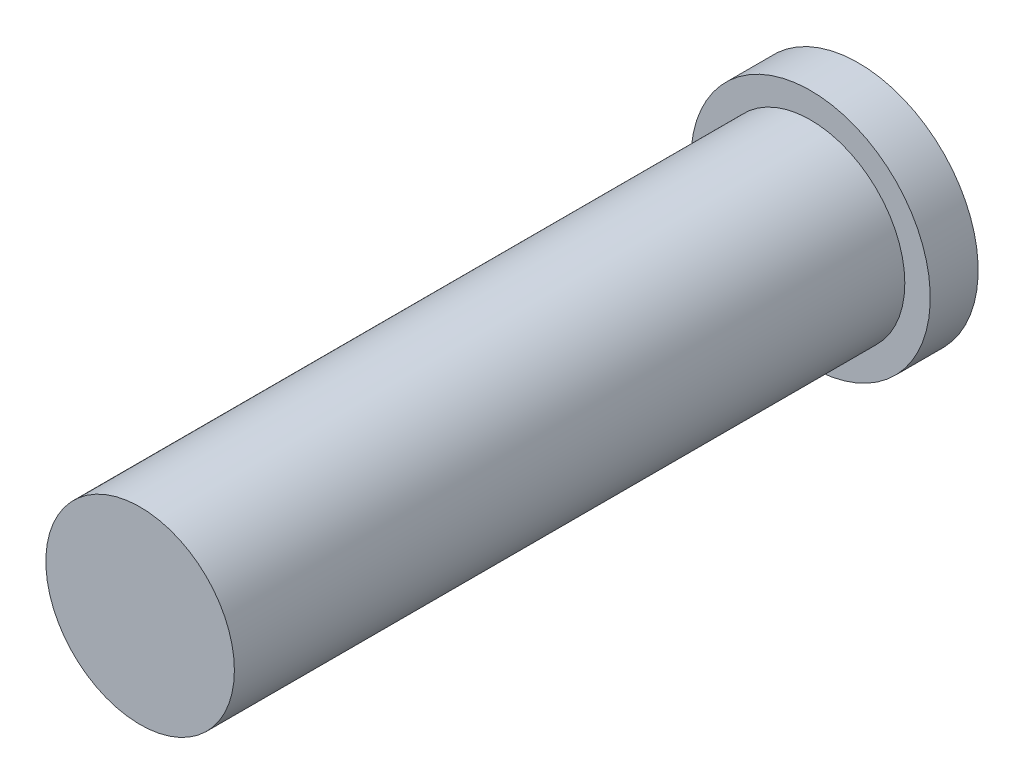
SolidWorks part; units mm, degrees
material "ABS"
ref_plane "Front Plane" through (0, 0, 0) normal (0, 0, 1) x (1, 0, 0)
ref_plane "Top Plane" through (0, 0, 0) normal (0, 1, 0) x (1, 0, 0)
ref_plane "Right Plane" through (0, 0, 0) normal (1, 0, 0) x (0, 0, -1)
sketch "Sketch1" plane through (0, 0, 0) normal (0, 0, 1) x (1, 0, 0)
  line L0 (11.0746, 1.623) -> (15.0746, 1.623) construction
  line L1 (15.5154, 2.1638) -> (14.2772, -0.5687)
  arc A1 (15.5154, 2.1638) -> (14.2772, -0.5687) centre (13.0746, 1.623) ccw
  point P10 (15.5154, 2.1638)
  point P13 (14.2772, -0.5687)
sketch "Sketch2" plane through (0, 0, 0) normal (0, 0, 1) x (1, 0, 0)
  circle A0 centre (13.0746, 1.623) radius 5
extrude "Boss-Extrude1" add sketch "Sketch2" along normal blind 35.56
extrude "Cut-Extrude1" cut sketch "Sketch1" along normal blind 25.4 and the other way through all contours A1 L1
sketch "Sketch3" plane through (0, 0, 0) normal (0, 0, -1) x (-1, 0, 0)
  circle A0 centre (-13.0746, 1.623) radius 6.35
extrude "Boss-Extrude2" add sketch "Sketch3" along normal blind 2.54
sketch "Sketch4" plane through (0, 0, -2.54) normal (0, 0, -1) x (-1, 0, 0)
  line L1 (-15.5154, 2.1638) -> (-14.2772, -0.5687)
  line L2 (-15.5154, 2.1638) -> (-14.2772, -0.5687)
  arc A1 (-14.2772, -0.5687) -> (-15.5154, 2.1638) centre (-13.0746, 1.623) ccw
  arc A2 (-14.2772, -0.5687) -> (-15.5154, 2.1638) centre (-13.0746, 1.623) ccw
  dimension "D1" = 0
extrude "Cut-Extrude2" cut sketch "Sketch4" against normal blind 2.54
sketch "Sketch5" plane through (0, 0, -2.54) normal (0, 0, -1) x (-1, 0, 0)
  circle A0 centre (-13.0746, 1.623) radius 2.5
extrude "Cut-Extrude3" cut sketch "Sketch5" against normal blind 28.575
